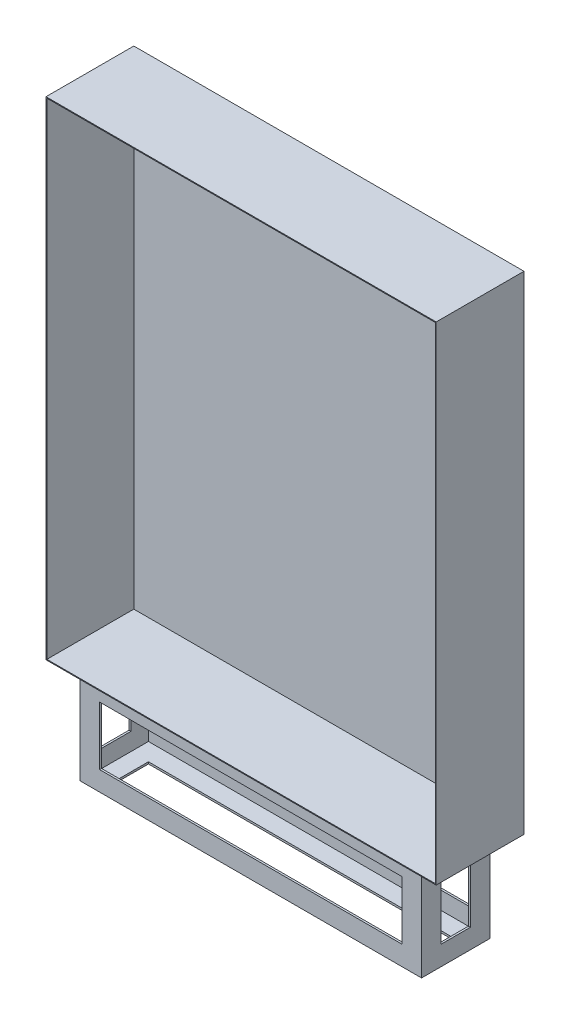
SolidWorks part; units mm, degrees
material "普通碳钢"
ref_plane "Front" through (0, 0, 0) normal (0, 0, 1) x (1, 0, 0)
ref_plane "Top" through (0, 0, 0) normal (0, 1, 0) x (1, 0, 0)
ref_plane "Right" through (0, 0, 0) normal (1, 0, 0) x (0, 0, -1)
sketch "草图1" plane through (0, 0, 0) normal (0, 0, 1) x (1, 0, 0)
  line L1 (0, 0) -> (800, 0)
  line L2 (0, 0) -> (0, 1000)
  line L3 (0, 1000) -> (800, 1000)
  line L4 (800, 0) -> (800, 1000)
  dimension "D1" = 1000
  dimension "D2" = 800
extrude "凸台-拉伸1" add sketch "草图1" along normal blind 180
shell "抽壳1" thickness 1.8
sketch "草图2" plane through (0, 0, 0) normal (0, -1, 0) x (1, 0, 0)
  line L6 (0, 160) -> (800, 160)
  line L7 (50, 160) -> (750, 160)
  line L13 (0, 20) -> (800, 20)
  line L14 (50, 20) -> (750, 20)
  line L20 (50, 180) -> (50, 0)
  line L21 (50, 160) -> (50, 20)
  line L26 (54, 156) -> (54, 24)
  line L27 (750, 180) -> (750, 0)
  line L28 (750, 160) -> (750, 20)
  line L29 (54, 24) -> (746, 24)
  line L30 (746, 156) -> (746, 24)
  line L31 (54, 156) -> (746, 156)
  dimension "D1" = 20
  dimension "D2" = 20
  dimension "D3" = 50
  dimension "D4" = 50
  dimension "D5" = 4
extrude "凸台-拉伸2" add sketch "草图2" along normal blind 200
sketch "草图3" plane through (0, -200, 0) normal (0, -1, 0) x (1, 0, 0)
  line L0 (90, 120) -> (90, 60)
  line L1 (90, 60) -> (710, 60)
  line L2 (710, 60) -> (710, 120)
  line L3 (710, 120) -> (90, 120)
  line L4 (50, 160) -> (50, 20)
  line L5 (50, 20) -> (750, 20)
  line L6 (750, 20) -> (750, 160)
  line L7 (750, 160) -> (50, 160)
  line L8 (50, 160) -> (50, 20)
  line L9 (50, 20) -> (750, 20)
  line L10 (750, 20) -> (750, 160)
  line L11 (750, 160) -> (50, 160)
  dimension "D1" = 0
  dimension "D2" = 40
extrude "凸台-拉伸3" add sketch "草图3" against normal blind 4
sketch "草图4" plane through (0, 0, 20) normal (0, 0, -1) x (-1, 0, 0)
  line L8 (-90, -160) -> (-90, -40)
  line L9 (-90, -40) -> (-710, -40)
  line L10 (-710, -40) -> (-710, -160)
  line L11 (-710, -160) -> (-90, -160)
  line L12 (-90, -160) -> (-90, -40)
  line L13 (-90, -40) -> (-710, -40)
  line L14 (-710, -40) -> (-710, -160)
  line L15 (-710, -160) -> (-90, -160)
  dimension "D1" = 40
extrude "切除-拉伸1" cut sketch "草图4" against normal up to surface (140 mm away) up to face at (400, -100, 160)
sketch "草图5" plane through (750, 0, 0) normal (1, 0, 0) x (0, 0, -1)
  line L8 (-60, -160) -> (-60, -40)
  line L9 (-60, -40) -> (-120, -40)
  line L10 (-120, -40) -> (-120, -160)
  line L11 (-120, -160) -> (-60, -160)
  line L12 (-60, -160) -> (-60, -40)
  line L13 (-60, -40) -> (-120, -40)
  line L14 (-120, -40) -> (-120, -160)
  line L15 (-120, -160) -> (-60, -160)
  dimension "D1" = 40
extrude "切除-拉伸2" cut sketch "草图5" against normal up to surface (700 mm away) up to face at (50, -100, 90)
